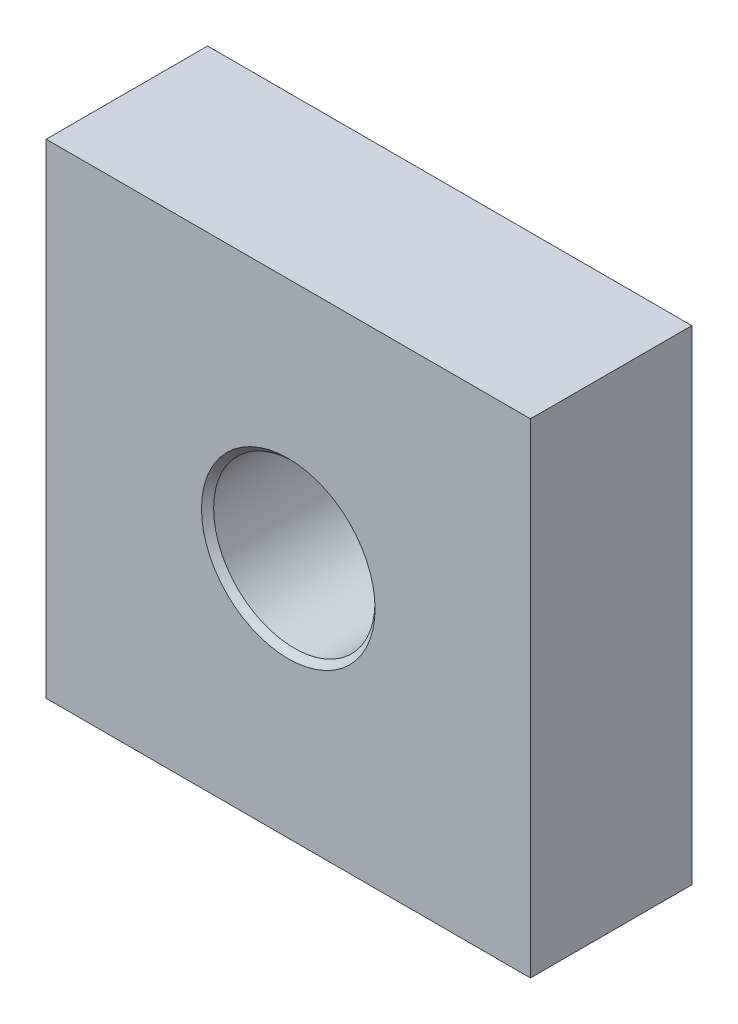
SolidWorks part; units mm, degrees
ref_plane "Front Plane" through (0, 0, 0) normal (0, 0, 1) x (1, 0, 0)
ref_plane "Top Plane" through (0, 0, 0) normal (0, 1, 0) x (1, 0, 0)
ref_plane "Right Plane" through (0, 0, 0) normal (1, 0, 0) x (0, 0, -1)
sketch "Sketch1" plane through (0, 0, 0) normal (0, 0, 1) x (1, 0, 0)
  line L0 (0, 29.7971) -> (0, -29.7971) construction
  line L1 (-60, 60) -> (60, 60)
  line L2 (-60, 60) -> (-60, -60)
  line L3 (-60, -60) -> (60, -60)
  line L4 (60, 60) -> (60, -60)
  line L5 (-23.2833, 0) -> (22.4518, 0) construction
  circle A0 centre (0, 0) radius 20
  dimension "D3" = 40
  dimension "D1" = 120
  dimension "D2" = 120
extrude "Extrude1" add sketch "Sketch1" along normal mid plane 40
chamfer "Frame Chamfer" distance 1.5 distance2 1.5 2 edges at (20, 0, -20) (20, 0, 20)
